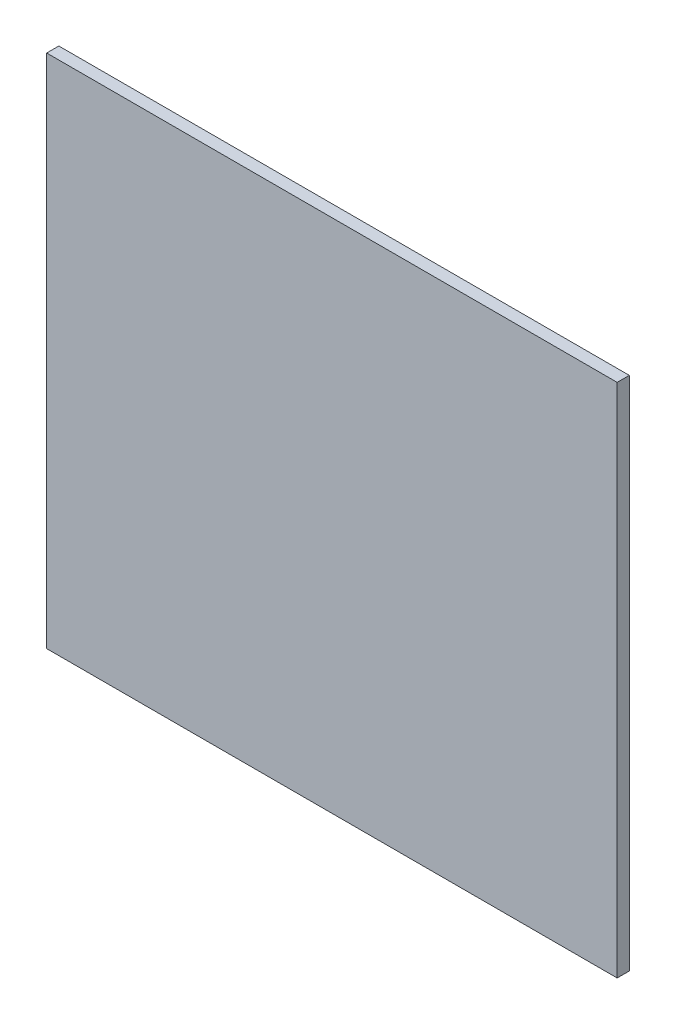
SolidWorks part; units mm, degrees
ref_plane "Plan de face" through (0, 0, 0) normal (0, 0, 1) x (1, 0, 0)
ref_plane "Plan de dessus" through (0, 0, 0) normal (0, 1, 0) x (1, 0, 0)
ref_plane "Plan de droite" through (0, 0, 0) normal (1, 0, 0) x (0, 0, -1)
sketch "Esquisse1" plane through (0, 0, 0) normal (0, 0, 1) x (1, 0, 0)
  line L1 (0, 0) -> (47, 0)
  line L2 (0, 0) -> (0, 42.5)
  line L3 (0, 42.5) -> (47, 42.5)
  line L4 (47, 0) -> (47, 42.5)
  dimension "D1" = 47
  dimension "D2" = 42.5
extrude "Boss.-Extru.1" add sketch "Esquisse1" along normal blind 1
